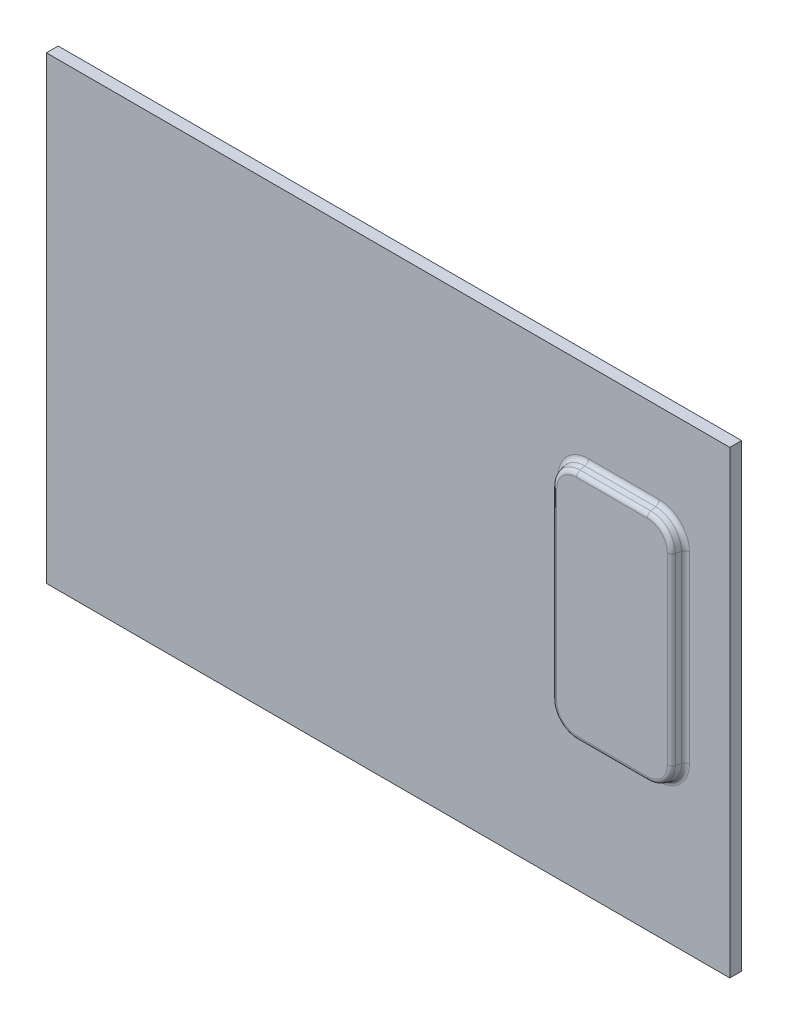
SolidWorks part; units mm, degrees
ref_plane "前视基准面" through (0, 0, 0) normal (0, 0, 1) x (1, 0, 0)
ref_plane "上视基准面" through (0, 0, 0) normal (0, 1, 0) x (1, 0, 0)
ref_plane "右视基准面" through (0, 0, 0) normal (1, 0, 0) x (0, 0, -1)
sketch "草图1" plane through (0, 0, 0) normal (0, 0, 1) x (1, 0, 0)
  line L1 (145, -97.5) -> (-145, -97.5)
  line L2 (145, -97.5) -> (145, 97.5)
  line L3 (145, 97.5) -> (-145, 97.5)
  line L4 (-145, -97.5) -> (-145, 97.5)
  line L5 (145, -97.5) -> (-145, 97.5) construction
  line L6 (145, 97.5) -> (-145, -97.5) construction
  point P0 (0, 0)
  dimension "D1" = 290
  dimension "D2" = 195
extrude "凸台-拉伸1" add sketch "草图1" along normal blind 5
sketch "草图2" plane through (0, 0, 5) normal (0, 0, 1) x (1, 0, 0)
  line L1 (75, 60.5) -> (125, 60.5)
  line L2 (75, 60.5) -> (75, -37.5)
  line L3 (75, -37.5) -> (125, -37.5)
  line L4 (125, 60.5) -> (125, -37.5)
  line L5 (75, 60.5) -> (125, -37.5) construction
  line L6 (75, -37.5) -> (125, 60.5) construction
  line L7 (-145, 97.5) -> (-145, -97.5) construction
  line L8 (145, 97.5) -> (-145, 97.5) construction
  point P0 (100, 11.5)
  dimension "D1" = 98
  dimension "D2" = 50
  dimension "D3" = 270
  dimension "D4" = 135
extrude "凸台-拉伸2" add sketch "草图2" along normal blind 5
fillet "圆角1" radius 10 4 edges at (125, 60.5, 7.5) (75, 60.5, 7.5) (125, -37.5, 7.5) (75, -37.5, 7.5)
draft "拔模1" type of draft neutral plane draft angle 15 faces to draft 8 face at (75, 11.5, 7.5) face at (78.9645, 56.5355, 7.5) face at (100, 60.5, 7.5) face at (121.0355, 56.5355, 7.5) face at (125, 11.5, 7.5) face at (121.0355, -33.5355, 7.5) face at (100, -37.5, 7.5) face at (78.9645, -33.5355, 7.5) neutral plane through (0, 0, 10) neutral plane normal (0, 0, 1) parameters "D1"=15
fillet "圆角2" radius 2 16 edges at (123.0184, -35.5184, 5) (100, -38.8397, 5) (76.9816, -35.5184, 5) (73.6603, 11.5, 5) (76.9816, 58.5184, 5) (100, 61.8397, 5) (123.0184, 58.5184, 5) (122.0711, -34.5711, 10) (100, -37.5, 10) (77.9289, -34.5711, 10) (75, 11.5, 10) (77.9289, 57.5711, 10) (100, 60.5, 10) (122.0711, 57.5711, 10) (126.3397, 11.5, 5) (125, 11.5, 10)
sketch "方向草图" plane through (0, 0, 5) normal (0, 0, 1) x (1, 0, 0)
  line L0 (127.8744, 50.5) -> (127.8744, -27.5) construction
  line L1 (115, -40.3744) -> (85, -40.3744) construction
  line L2 (72.1256, -27.5) -> (72.1256, 50.5) construction
  line L3 (85, 63.3744) -> (115, 63.3744) construction
  line L4 (-145, 97.5) -> (-145, -97.5) construction
  line L5 (-145, -97.5) -> (145, -97.5) construction
  line L6 (145, -97.5) -> (145, 97.5) construction
  line L7 (145, 97.5) -> (-145, 97.5) construction
  line L8 (127.8744, 50.5) -> (127.8744, -27.5)
  line L9 (115, -40.3744) -> (85, -40.3744)
  line L10 (72.1256, -27.5) -> (72.1256, 50.5)
  line L11 (85, 63.3744) -> (115, 63.3744)
  line L12 (-145, 97.5) -> (-145, -97.5) construction
  line L13 (-145, -97.5) -> (145, -97.5) construction
  line L14 (145, -97.5) -> (145, 97.5) construction
  line L15 (145, 97.5) -> (-145, 97.5) construction
  arc A0 (115, -40.3744) -> (127.8744, -27.5) centre (115, -27.5) ccw construction
  arc A1 (72.1256, -27.5) -> (85, -40.3744) centre (85, -27.5) ccw construction
  arc A2 (85, 63.3744) -> (72.1256, 50.5) centre (85, 50.5) ccw construction
  arc A3 (127.8744, 50.5) -> (115, 63.3744) centre (115, 50.5) ccw construction
  arc A4 (115, -40.3744) -> (127.8744, -27.5) centre (115, -27.5) ccw
  arc A5 (72.1256, -27.5) -> (85, -40.3744) centre (85, -27.5) ccw
  arc A6 (85, 63.3744) -> (72.1256, 50.5) centre (85, 50.5) ccw
  arc A7 (127.8744, 50.5) -> (115, 63.3744) centre (115, 50.5) ccw
  point P14 (0, 0)
other "成形工具1"
